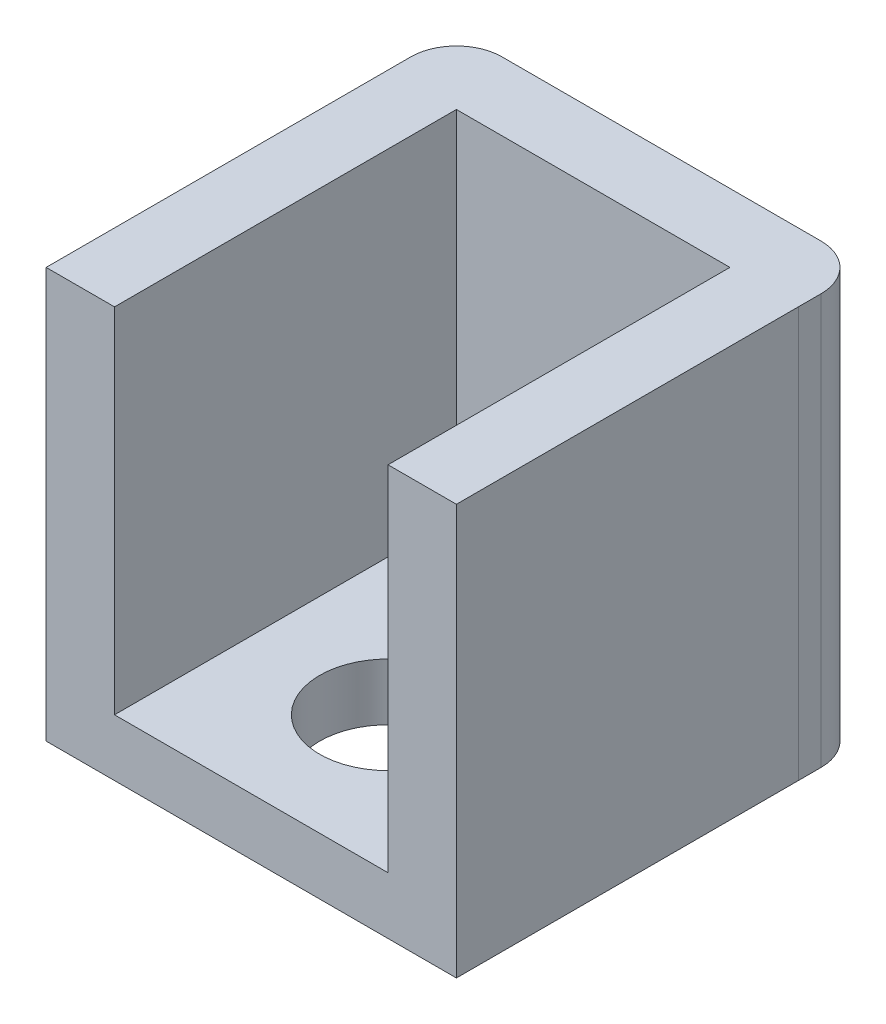
SolidWorks part; units mm, degrees
ref_plane "Front Plane" through (0, 0, 0) normal (0, 0, 1) x (1, 0, 0)
ref_plane "Top Plane" through (0, 0, 0) normal (0, 1, 0) x (1, 0, 0)
ref_plane "Right Plane" through (0, 0, 0) normal (1, 0, 0) x (0, 0, -1)
sketch "Sketch1" plane through (0, 0, 0) normal (0, 0, 1) x (1, 0, 0)
  line L1 (0, 0) -> (18, 0)
  line L2 (0, 0) -> (0, 18)
  line L3 (0, 18) -> (18, 18)
  line L4 (18, 0) -> (18, 18)
  dimension "D1" = 18
  dimension "D2" = 18
extrude "Boss-Extrude2" add sketch "Sketch1" along normal blind 3
sketch "Sketch2" plane through (0, 0, 3) normal (0, 0, 1) x (1, 0, 0)
  line L0 (18, 18) -> (0, 18) construction
  line L1 (14.9999, 18) -> (17.9999, 18)
  line L2 (14.9999, 18) -> (14.9999, 0)
  line L3 (14.9999, 0) -> (17.9999, 0)
  line L4 (17.9999, 18) -> (17.9999, 0)
  line L5 (0, 0) -> (18, 0) construction
  dimension "D1" = 3
extrude "Boss-Extrude3" add sketch "Sketch2" along normal blind 15
sketch "Sketch3" plane through (0, 0, 3) normal (0, 0, 1) x (1, 0, 0)
  line L0 (14.9999, 18) -> (0, 18) construction
  line L1 (0, 0) -> (3, 0)
  line L2 (0, 0) -> (0, 18)
  line L3 (0, 18) -> (3, 18)
  line L4 (3, 0) -> (3, 18)
  dimension "D1" = 3
extrude "Boss-Extrude4" add sketch "Sketch3" along normal blind 15
ref_plane "Plane1" through (3, 0, 18) normal (0, 1, 0) x (1, 0, 0)
sketch "Sketch5" plane through (0, 0, 3) normal (0, 0, 1) x (1, 0, 0)
  line L0 (7.95, 0) -> (-1.95, 0) construction
  line L1 (3, 0) -> (14.9999, 0)
  line L2 (3, 0) -> (3, 2.5)
  line L3 (3, 2.5) -> (14.9999, 2.5)
  line L4 (14.9999, 0) -> (14.9999, 2.5)
  line L5 (3, 0) -> (3, 18) construction
  line L6 (14.9999, 18) -> (14.9999, 0) construction
  dimension "D1" = 2.5
extrude "Boss-Extrude5" add sketch "Sketch5" along normal blind 15
fillet "Fillet1" radius 2 1 edges at (0, 9, 0)
fillet "Fillet2" radius 2 1 edges at (18, 9, 0)
sketch "Sketch6" plane through (0, 0, 0) normal (0, -1, 0) x (1, 0, 0)
  line L0 (17.4142, 0.5858) -> (0, 18) construction
  line L1 (17.9999, 18) -> (0.5858, 0.5858) construction
  line L2 (9, 0) -> (9, 18) construction
  line L3 (2, 0) -> (16, 0) construction
  line L4 (0, 18) -> (17.9999, 18) construction
  line L5 (17.9999, 12) -> (0, 12) construction
  line L6 (17.9999, 18) -> (17.9999, 3) construction
  line L7 (0, 18) -> (0, 2) construction
  arc A0 (16, 0) -> (18, 2) centre (16, 2) ccw construction
  arc A1 (0, 2) -> (2, 0) centre (2, 2) ccw construction
  circle A2 centre (9, 12) radius 3
  dimension "D1" = 6
extrude "Cut-Extrude1" cut sketch "Sketch6" against normal through all
